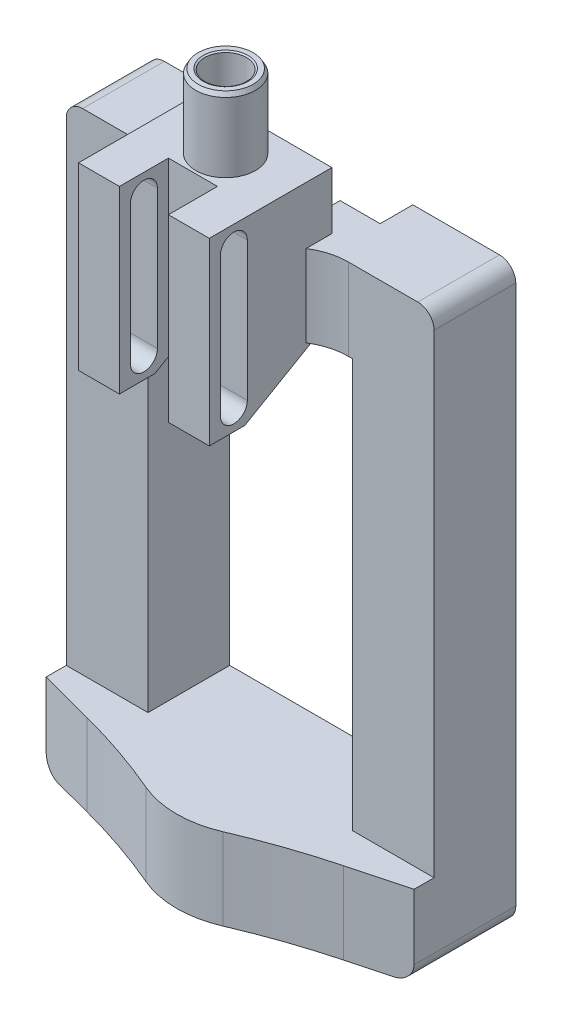
SolidWorks part; units mm, degrees
ref_plane "Front Plane" through (0, 0, 0) normal (0, 0, 1) x (1, 0, 0)
ref_plane "Top Plane" through (0, 0, 0) normal (0, 1, 0) x (1, 0, 0)
ref_plane "Right Plane" through (0, 0, 0) normal (1, 0, 0) x (0, 0, -1)
sketch "Sketch2" plane through (0, 0, 0) normal (0, 0, 1) x (1, 0, 0)
  line L1 (-12.5, 60) -> (12.5, 60)
  line L2 (-12.5, 60) -> (-12.5, 10)
  line L3 (-12.5, 10) -> (12.5, 10)
  line L4 (12.5, 60) -> (12.5, 10)
  line L5 (-22.5, 70) -> (22.5, 70)
  line L6 (-22.5, 70) -> (-22.5, 0)
  line L7 (-22.5, 0) -> (22.5, 0)
  line L8 (22.5, 70) -> (22.5, 0)
  point P4 (0, 10)
  point P10 (0, 0)
  dimension "D1" = 60
  dimension "D2" = 25
  dimension "D3" = 10
  dimension "D4" = 10
  dimension "D5" = 10
extrude "Boss-Extrude2" add sketch "Sketch2" along normal blind 10
sketch "Sketch3" plane through (0, 70, 0) normal (0, 1, 0) x (1, 0, 0)
  line L0 (-9.9, 0) -> (-9.9, -4)
  line L1 (22.5, 0) -> (-22.5, 0) construction
  line L2 (-9.9, -4) -> (-5, -4)
  line L3 (-5, -4) -> (-5, -8)
  line L4 (-5, -8) -> (5, -8)
  line L5 (5, -8) -> (5, -4)
  line L6 (5, -4) -> (9.9, -4)
  line L7 (9.9, -4) -> (9.9, 0)
  line L8 (-9.9, 0) -> (9.9, 0)
  point P4 (0, -8)
  dimension "D1" = 8
  dimension "D2" = 4
  dimension "D3" = 10
  dimension "D4" = 19.8
extrude "Cut-Extrude1" cut sketch "Sketch3" against normal up to next
sketch "Sketch4" plane through (0, 70, 0) normal (0, 1, 0) x (1, 0, 0)
  line L0 (-12, -10) -> (12, -10)
  line L1 (22.5, -10) -> (-22.5, -10) construction
  arc A0 (12, -10) -> (4.8, -15.4) centre (12, -17.5) ccw
  arc A1 (4.8, -15.4) -> (-4.8, -15.4) centre (0, -14) cw
  arc A2 (-4.8, -15.4) -> (-12, -10) centre (-12, -17.5) ccw
  circle A3 centre (0, -14) radius 3.65 construction
  dimension "D1" = 7.3
  dimension "D4" = 5
  dimension "D2" = 14
  dimension "D3" = 7.5
extrude "Boss-Extrude3" add sketch "Sketch4" against normal up to surface (10 mm away) up to face at (0, 60, 4.3333)
sketch "Sketch6" plane through (0, 70, 0) normal (0, 1, 0) x (1, 0, 0)
  circle A0 centre (0, -13) radius 3.65
  circle A1 centre (0, -13) radius 4.85 construction
  dimension "D1" = 7.3
  dimension "D2" = 9.7
  dimension "D3" = 13
extrude "Boss-Extrude4" add sketch "Sketch6" along normal blind 16
sketch "Sketch7" plane through (0, 0, 0) normal (0, -1, 0) x (1, 0, 0)
  line L1 (63, 1.7311) -> (15.6931, 14.2587) construction
  line L2 (-15.6931, 14.2587) -> (-63, 1.7311) construction
  line L3 (63, 1.7311) -> (15.6931, 14.2587) construction
  line L4 (-15.6931, 14.2587) -> (-63, 1.7311) construction
  line L5 (-22.5, 10) -> (-22.5, 12.4561)
  line L6 (-22.5, 12.4561) -> (-15.6931, 14.2587)
  line L7 (15.6931, 14.2587) -> (22.5, 12.4561)
  line L8 (22.5, 12.4561) -> (22.5, 10)
  line L9 (22.5, 10) -> (-22.5, 10)
  arc A6 (12.8214, 17.2181) -> (15.6931, 14.2587) centre (16.7171, 18.1254) ccw construction
  arc A7 (-15.6931, 14.2587) -> (-12.8214, 17.2181) centre (-16.7171, 18.1254) ccw construction
  arc A8 (12.8214, 17.2181) -> (15.6931, 14.2587) centre (16.7171, 18.1254) ccw construction
  arc A9 (-15.6931, 14.2587) -> (-12.8214, 17.2181) centre (-16.7171, 18.1254) ccw construction
  arc A11 (-15.6931, 14.2587) -> (-4.7143, 18.0352) centre (-36.2283, 91.8038) ccw
  arc A12 (-4.7143, 18.0352) -> (4.7143, 18.0352) centre (0, 7) cw
  arc A13 (4.7143, 18.0352) -> (15.6931, 14.2587) centre (36.2283, 91.8038) ccw
  dimension "D2" = 12
  dimension "D1" = 7
extrude "Boss-Extrude5" add sketch "Sketch7" against normal up to surface (10 mm away) up to face at (0, 10, 5)
sketch "Sketch8" plane through (0, 0, 0) normal (1, 0, 0) x (0, 0, -1)
  line L0 (-19, 70) -> (-19, 77) construction
  line L1 (-15.4, 70) -> (-19, 70) construction
  line L2 (-19, 60) -> (-19, 55) construction
  line L3 (-19, 60) -> (-15.4, 60) construction
  line L4 (-19, 77) -> (-23, 77)
  line L5 (-23, 77) -> (-23, 55)
  line L6 (-23, 55) -> (-18.6603, 55)
  line L7 (-18.6603, 55) -> (-10, 60)
  line L8 (-19, 70) -> (-19, 60) construction
  line L11 (-19, 77) -> (-10, 77)
  line L12 (-10, 60) -> (-10, 70) construction
  line L14 (-10, 60) -> (-10, 70)
  line L15 (-10, 70) -> (-8, 70)
  line L16 (-10, 70) -> (0, 70) construction
  line L17 (-8, 70) -> (-8, 77)
  line L19 (-8, 77) -> (-10, 77)
  dimension "D1" = 30
  dimension "D2" = 5
  dimension "D3" = 7
  dimension "D5" = 4
extrude "Boss-Extrude8" add sketch "Sketch8" along normal mid plane 16
sketch "Sketch9" plane through (0, 0, 23) normal (0, 0, 1) x (1, 0, 0)
  line L0 (8, 77) -> (-8, 77) construction
  line L1 (-3, 77) -> (3, 77)
  line L2 (-3, 77) -> (-3, 55)
  line L3 (-3, 55) -> (3, 55)
  line L4 (3, 77) -> (3, 55)
  line L5 (8, 55) -> (-8, 55) construction
  point P8 (0, 55)
  dimension "D1" = 6
extrude "Cut-Extrude2" cut sketch "Sketch9" against normal blind 6
sketch "Sketch10" plane through (-8, 0, 0) normal (-1, 0, 0) x (0, 0, 1)
  line L0 (23, 55) -> (23, 77) construction
  line L2 (17, 55.9585) -> (17, 77) construction
  line L3 (23, 55) -> (23, 77) construction
  line L5 (17, 55.9585) -> (17, 77) construction
  line L6 (18.35, 74.5) -> (18.35, 57.5)
  line L7 (21.65, 57.5) -> (21.65, 74.5)
  line L8 (17, 66.4793) -> (23, 66.4793) construction
  line L9 (8, 77) -> (23, 77) construction
  arc A0 (18.35, 57.5) -> (21.65, 57.5) centre (20, 57.5) ccw
  arc A1 (21.65, 74.5) -> (18.35, 74.5) centre (20, 74.5) ccw
  point P14 (20, 66.4793)
  dimension "D1" = 3.3
  dimension "D2" = 17
  dimension "D3" = 2.5
extrude "Cut-Extrude3" cut sketch "Sketch10" against normal through all both and the other way through all
sketch "Sketch11" plane through (0, 86, 0) normal (0, 1, 0) x (1, 0, 0)
  circle A0 centre (0, -13) radius 3.65 construction
  circle A1 centre (0, -13) radius 3.65 construction
  circle A2 centre (0, -13) radius 2.55
  dimension "D1" = 5.1
extrude "Cut-Extrude4" cut sketch "Sketch11" against normal blind 13
chamfer "Chamfer1" distance 0.2 angle 30 1 edges at (0, 86, 15.55)
chamfer "Chamfer2" distance 0.5 angle 30 1 edges at (0, 86, 16.65)
fillet "Fillet1" radius 2 4 edges at (-22.5, 70, 5) (-22.5, 0, 6.2281) (22.5, 0, 6.2281) (22.5, 70, 5)
